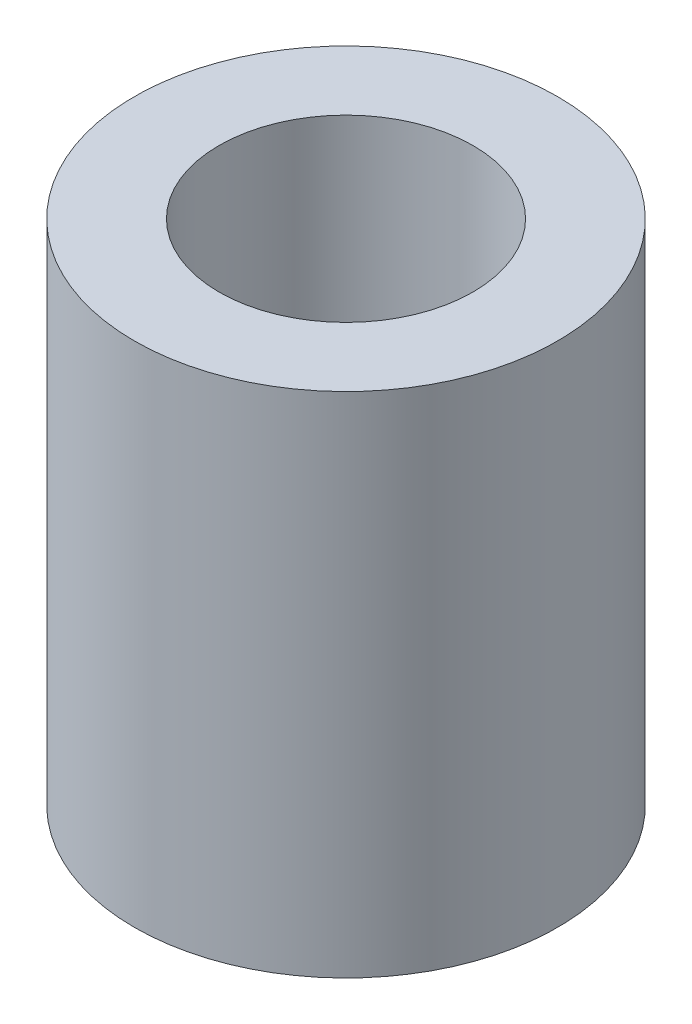
SolidWorks part; units mm, degrees
ref_plane "Front Plane" through (0, 0, 0) normal (0, 0, 1) x (1, 0, 0)
ref_plane "Top Plane" through (0, 0, 0) normal (0, 1, 0) x (1, 0, 0)
ref_plane "Right Plane" through (0, 0, 0) normal (1, 0, 0) x (0, 0, -1)
sketch "Sketch1" plane through (0, 0, 0) normal (0, 1, 0) x (1, 0, 0)
  circle A0 centre (0, 0) radius 7.5
  circle A1 centre (0, 0) radius 4.5
extrude "Boss-Extrude1" add sketch "Sketch1" along normal blind 18
